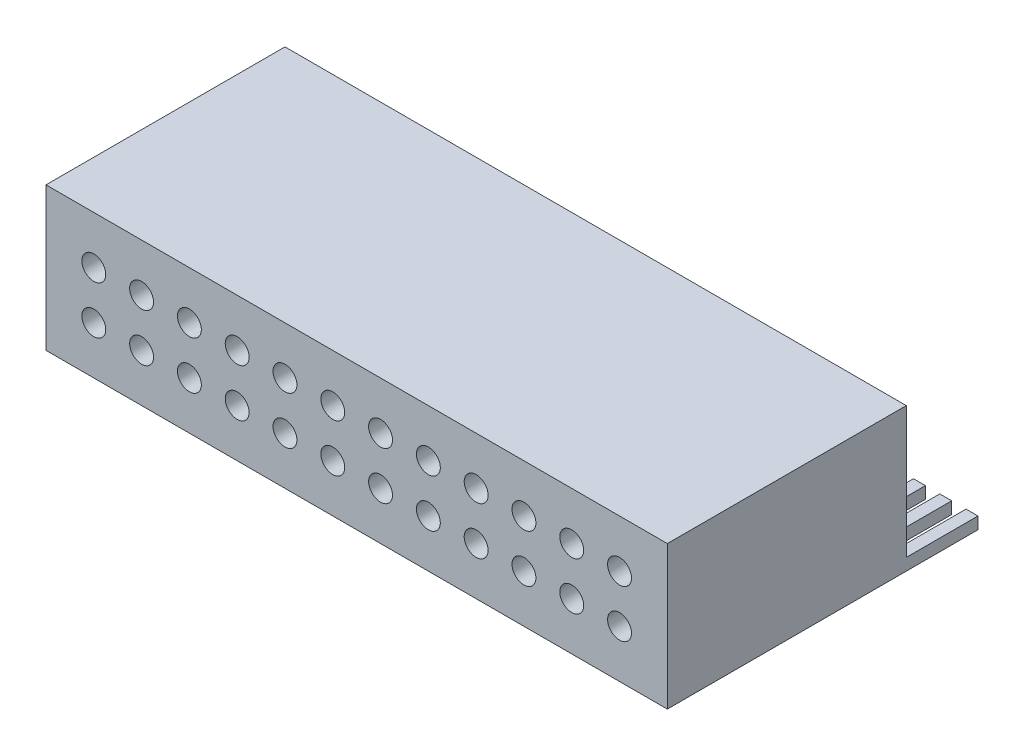
SolidWorks part; units mm, degrees
ref_plane "Front Plane" through (0, 0, 0) normal (0, 0, 1) x (1, 0, 0)
ref_plane "Top Plane" through (0, 0, 0) normal (0, 1, 0) x (1, 0, 0)
ref_plane "Right Plane" through (0, 0, 0) normal (1, 0, 0) x (0, 0, -1)
sketch "Sketch2" plane through (0, 0, 0) normal (0, 0, 1) x (1, 0, 0)
  line L1 (0, 0) -> (26, 0)
  line L2 (0, 0) -> (0, 6)
  line L3 (0, 6) -> (26, 6)
  line L4 (26, 0) -> (26, 6)
  dimension "D1" = 26
  dimension "D2" = 6
extrude "Boss-Extrude1" add sketch "Sketch2" along normal blind 10
sketch "Sketch3" plane through (0, 0, 10) normal (0, 0, 1) x (1, 0, 0)
  line L0 (0, 2) -> (26, 2) construction
  line L1 (0, 6) -> (0, 0) construction
  line L2 (26, 0) -> (26, 6) construction
  line L3 (0, 3) -> (26, 3) construction
  line L4 (26, 6) -> (0, 6) construction
  line L5 (0, 0) -> (26, 0) construction
  line L6 (2, 6) -> (2, 0) construction
  line L7 (2, 2) -> (4, 2) construction
  circle A0 centre (2, 2) radius 0.5
  circle A1 centre (4, 2) radius 0.5
  circle A2 centre (6, 2) radius 0.5
  circle A3 centre (8, 2) radius 0.5
  circle A4 centre (10, 2) radius 0.5
  circle A5 centre (12, 2) radius 0.5
  circle A6 centre (14, 2) radius 0.5
  circle A7 centre (16, 2) radius 0.5
  circle A8 centre (18, 2) radius 0.5
  circle A9 centre (20, 2) radius 0.5
  circle A10 centre (22, 2) radius 0.5
  circle A11 centre (24, 2) radius 0.5
  circle A12 centre (24, 4) radius 0.5
  circle A13 centre (22, 4) radius 0.5
  circle A14 centre (20, 4) radius 0.5
  circle A15 centre (18, 4) radius 0.5
  circle A16 centre (16, 4) radius 0.5
  circle A17 centre (14, 4) radius 0.5
  circle A18 centre (12, 4) radius 0.5
  circle A19 centre (10, 4) radius 0.5
  circle A20 centre (8, 4) radius 0.5
  circle A21 centre (6, 4) radius 0.5
  circle A22 centre (4, 4) radius 0.5
  circle A23 centre (2, 4) radius 0.5
  dimension "D1" = 1
  dimension "D2" = 2
  dimension "D3" = 2
  dimension "D5" = 2
  dimension "D4" = 12
extrude "Cut-Extrude1" cut sketch "Sketch3" against normal blind 5
sketch "Sketch4" plane through (0, 0, 0) normal (0, -1, 0) x (-1, 0, 0)
  line L0 (-24.9, 0) -> (-24.9, 3)
  line L1 (-26, 0) -> (-25.5, 0)
  line L2 (-26, 0) -> (-26, 3)
  line L3 (-26, 3) -> (-25.5, 3)
  line L4 (-25.5, 0) -> (-25.5, 3)
  line L5 (-24.9, 3) -> (-24.4, 3)
  line L6 (-24.4, 0) -> (-24.4, 3)
  line L7 (-24.9, 0) -> (-24.4, 0)
  line L8 (-23.8, 0) -> (-23.8, 3)
  line L9 (-23.8, 3) -> (-23.3, 3)
  line L10 (-23.3, 0) -> (-23.3, 3)
  line L11 (-23.8, 0) -> (-23.3, 0)
  line L12 (-22.7, 0) -> (-22.7, 3)
  line L13 (-22.7, 3) -> (-22.2, 3)
  line L14 (-22.2, 0) -> (-22.2, 3)
  line L15 (-22.7, 0) -> (-22.2, 0)
  line L16 (-21.6, 0) -> (-21.6, 3)
  line L17 (-21.6, 3) -> (-21.1, 3)
  line L18 (-21.1, 0) -> (-21.1, 3)
  line L19 (-21.6, 0) -> (-21.1, 0)
  line L20 (-20.5, 0) -> (-20.5, 3)
  line L21 (-20.5, 3) -> (-20, 3)
  line L22 (-20, 0) -> (-20, 3)
  line L23 (-20.5, 0) -> (-20, 0)
  line L24 (-19.4, 0) -> (-19.4, 3)
  line L25 (-19.4, 3) -> (-18.9, 3)
  line L26 (-18.9, 0) -> (-18.9, 3)
  line L27 (-19.4, 0) -> (-18.9, 0)
  line L28 (-18.3, 0) -> (-18.3, 3)
  line L29 (-18.3, 3) -> (-17.8, 3)
  line L30 (-17.8, 0) -> (-17.8, 3)
  line L31 (-18.3, 0) -> (-17.8, 0)
  line L32 (-17.2, 0) -> (-17.2, 3)
  line L33 (-17.2, 3) -> (-16.7, 3)
  line L34 (-16.7, 0) -> (-16.7, 3)
  line L35 (-17.2, 0) -> (-16.7, 0)
  line L36 (-16.1, 0) -> (-16.1, 3)
  line L37 (-16.1, 3) -> (-15.6, 3)
  line L38 (-15.6, 0) -> (-15.6, 3)
  line L39 (-16.1, 0) -> (-15.6, 0)
  line L40 (-15, 0) -> (-15, 3)
  line L41 (-15, 3) -> (-14.5, 3)
  line L42 (-14.5, 0) -> (-14.5, 3)
  line L43 (-15, 0) -> (-14.5, 0)
  line L44 (-13.9, 0) -> (-13.9, 3)
  line L45 (-13.9, 3) -> (-13.4, 3)
  line L46 (-13.4, 0) -> (-13.4, 3)
  line L47 (-13.9, 0) -> (-13.4, 0)
  line L48 (-12.8, 0) -> (-12.8, 3)
  line L49 (-12.8, 3) -> (-12.3, 3)
  line L50 (-12.3, 0) -> (-12.3, 3)
  line L51 (-12.8, 0) -> (-12.3, 0)
  line L52 (-11.7, 0) -> (-11.7, 3)
  line L53 (-11.7, 3) -> (-11.2, 3)
  line L54 (-11.2, 0) -> (-11.2, 3)
  line L55 (-11.7, 0) -> (-11.2, 0)
  line L56 (-10.6, 0) -> (-10.6, 3)
  line L57 (-10.6, 3) -> (-10.1, 3)
  line L58 (-10.1, 0) -> (-10.1, 3)
  line L59 (-10.6, 0) -> (-10.1, 0)
  line L60 (-9.5, 0) -> (-9.5, 3)
  line L61 (-9.5, 3) -> (-9, 3)
  line L62 (-9, 0) -> (-9, 3)
  line L63 (-9.5, 0) -> (-9, 0)
  line L64 (-8.4, 0) -> (-8.4, 3)
  line L65 (-8.4, 3) -> (-7.9, 3)
  line L66 (-7.9, 0) -> (-7.9, 3)
  line L67 (-8.4, 0) -> (-7.9, 0)
  line L68 (-7.3, 0) -> (-7.3, 3)
  line L69 (-7.3, 3) -> (-6.8, 3)
  line L70 (-6.8, 0) -> (-6.8, 3)
  line L71 (-7.3, 0) -> (-6.8, 0)
  line L72 (-6.2, 0) -> (-6.2, 3)
  line L73 (-6.2, 3) -> (-5.7, 3)
  line L74 (-5.7, 0) -> (-5.7, 3)
  line L75 (-6.2, 0) -> (-5.7, 0)
  line L76 (-5.1, 0) -> (-5.1, 3)
  line L77 (-5.1, 3) -> (-4.6, 3)
  line L78 (-4.6, 0) -> (-4.6, 3)
  line L79 (-5.1, 0) -> (-4.6, 0)
  line L80 (-4, 0) -> (-4, 3)
  line L81 (-4, 3) -> (-3.5, 3)
  line L82 (-3.5, 0) -> (-3.5, 3)
  line L83 (-4, 0) -> (-3.5, 0)
  line L84 (-2.9, 0) -> (-2.9, 3)
  line L85 (-2.9, 3) -> (-2.4, 3)
  line L86 (-2.4, 0) -> (-2.4, 3)
  line L87 (-2.9, 0) -> (-2.4, 0)
  line L88 (-1.8, 0) -> (-1.8, 3)
  line L89 (-1.8, 3) -> (-1.3, 3)
  line L90 (-1.3, 0) -> (-1.3, 3)
  line L91 (-1.8, 0) -> (-1.3, 0)
  line L92 (-0.7, 0) -> (-0.7, 3)
  line L93 (-0.7, 3) -> (-0.2, 3)
  line L94 (-0.2, 0) -> (-0.2, 3)
  line L95 (-0.7, 0) -> (-0.2, 0)
  line L96 (-26, 0) -> (-24.9, 0) construction
  dimension "D1" = 3
  dimension "D2" = 0.5
  dimension "D4" = 1.1
  dimension "D3" = 24
extrude "Boss-Extrude2" add sketch "Sketch4" against normal blind 0.5
sketch "Sketch5" plane through (0, 0, 10) normal (0, 0, 1) x (1, 0, 0)
  point P0 (2, 4)
  point P1 (4, 4)
  point P3 (6, 4)
  point P5 (8, 4)
  point P7 (10, 4)
  point P9 (12, 4)
  point P11 (14, 4)
  point P13 (16, 4)
  point P15 (18, 4)
  point P17 (20, 4)
  point P19 (22, 4)
  point P21 (24, 4)
  point P23 (24, 2)
  point P25 (22, 2)
  point P27 (20, 2)
  point P29 (18, 2)
  point P31 (16, 2)
  point P33 (14, 2)
  point P35 (12, 2)
  point P37 (10, 2)
  point P39 (8, 2)
  point P41 (6, 2)
  point P43 (4, 2)
  point P45 (2, 2)
